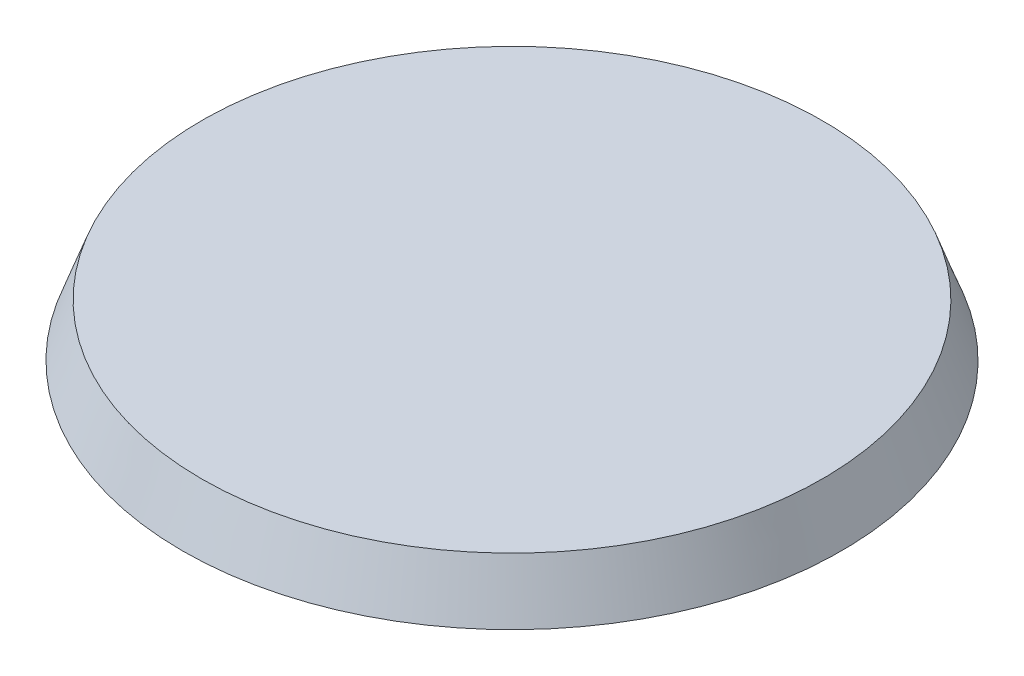
SolidWorks part; units mm, degrees
ref_plane "Front Plane" through (0, 0, 0) normal (0, 0, 1) x (1, 0, 0)
ref_plane "Top Plane" through (0, 0, 0) normal (0, 1, 0) x (1, 0, 0)
ref_plane "Right Plane" through (0, 0, 0) normal (1, 0, 0) x (0, 0, -1)
sketch "Sketch1" plane through (0, 0, 0) normal (0, 1, 0) x (1, 0, 0)
  circle A0 centre (0, 0) radius 25
  dimension "D1" = 50
extrude "Boss-Extrude1" add sketch "Sketch1" along normal blind 4 draft 20
